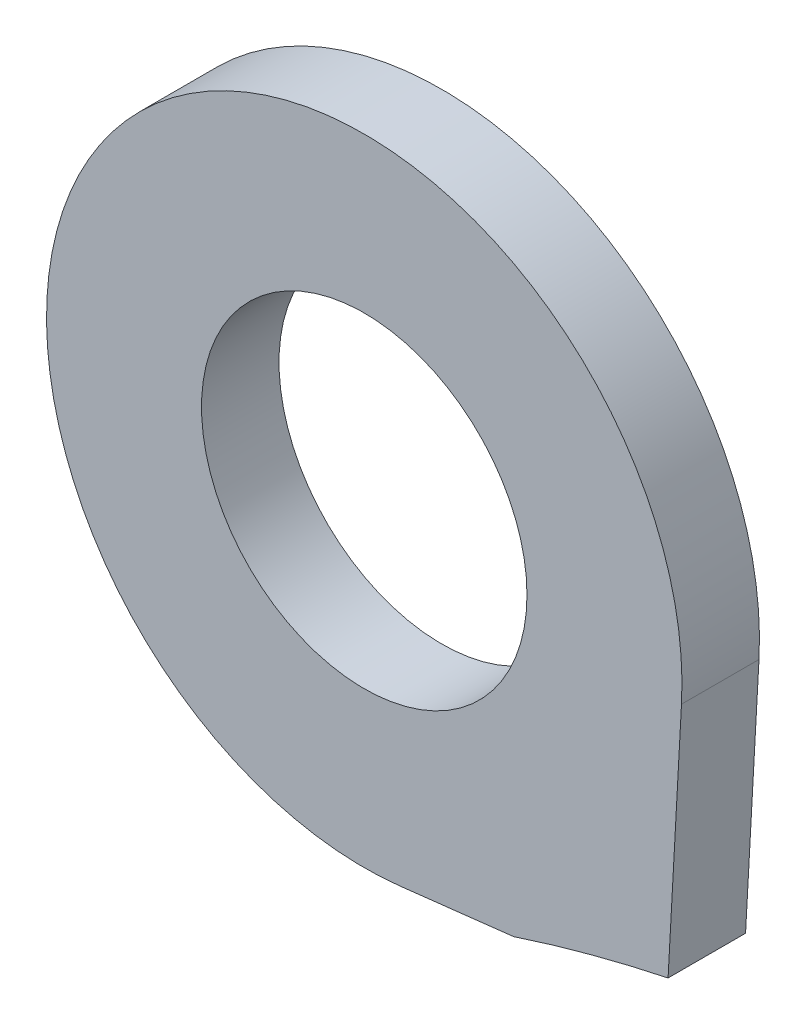
SolidWorks part; units mm, degrees
ref_plane "Front Plane" through (0, 0, 0) normal (0, 0, 1) x (1, 0, 0)
ref_plane "Top Plane" through (0, 0, 0) normal (0, 1, 0) x (1, 0, 0)
ref_plane "Right Plane" through (0, 0, 0) normal (1, 0, 0) x (0, 0, -1)
sketch "Sketch1" plane through (0, 0, 0) normal (0, 0, 1) x (1, 0, 0)
  line L0 (-5.8226, -27.1559) -> (-7.2831, -27.3233)
  line L1 (-3.6562, -23.4755) -> (-3.8295, -26.6219)
  line L3 (-4.1606, -27.9234) -> (-4.8851, -28.1175) construction
  line L5 (-4.5229, -28.0204) -> (-4.8334, -26.8613) construction
  circle A0 centre (-7.75, -23.25) radius 2.1 construction
  circle A1 centre (-7.75, -23.25) radius 2.1
  arc A2 (-7.2831, -27.3233) -> (-3.6562, -23.4755) centre (-7.75, -23.25) cw
  arc A3 (-5.8226, -27.1559) -> (-3.8295, -26.6219) centre (0, -44.9) cw
  circle A5 centre (0, -44.9) radius 18.475 construction
  circle A6 centre (0, -44.9) radius 18.475 construction
  point P9 (-4.0359, -26.7542)
  point P16 (-7.2174, -27.3153)
  point P19 (-5.767, -27.1377)
  point P20 (0, 0)
  point P21 (-7.2728, -27.3221)
  dimension "D1" = 2
  dimension "D2" = 0.2
  dimension "D3" = 1.47
extrude "Boss-Extrude1" add sketch "Sketch1" along normal blind 1
sketch "Sketch2" plane through (0, 0, 1) normal (0, 0, 1) x (1, 0, 0)
  line L0 (-5.8226, -27.1559) -> (-5.9521, -26.673)
  line L1 (-5.9521, -26.673) -> (-3.9589, -26.1389)
  line L2 (-3.9589, -26.1389) -> (-3.8295, -26.6219)
  arc A0 (-3.8295, -26.6219) -> (-5.8226, -27.1559) centre (0, -44.9) ccw construction
  arc A1 (-3.8295, -26.6219) -> (-5.8226, -27.1559) centre (0, -44.9) ccw
  point P3 (-3.9187, -26.193)
  dimension "D1" = 0.5
